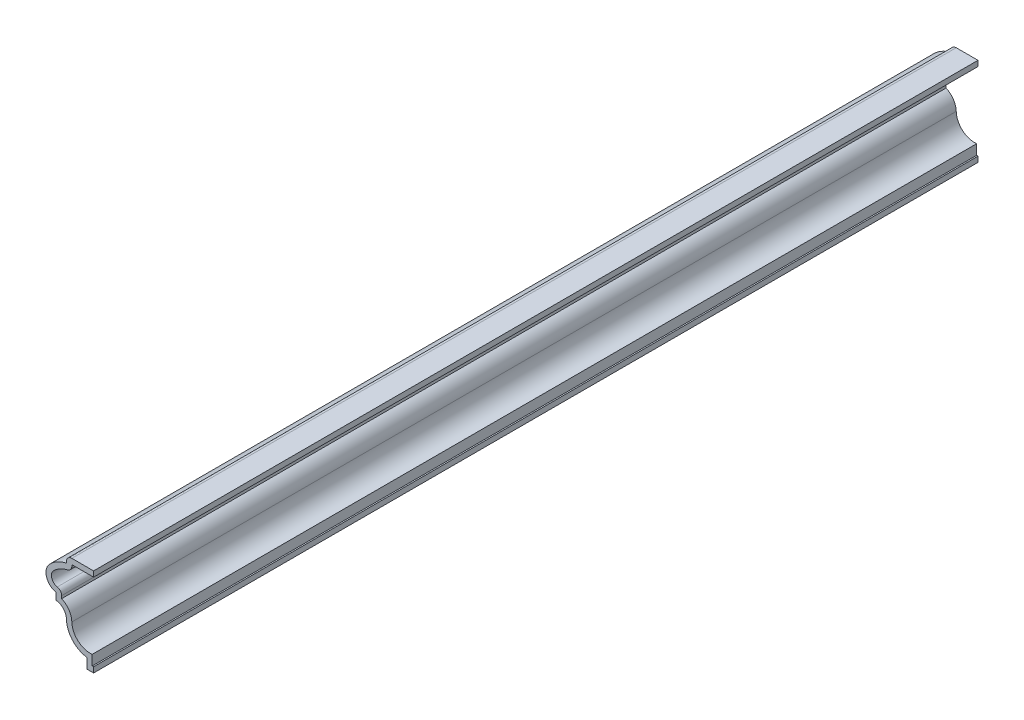
SolidWorks part; units mm, degrees
ref_plane "Front Plane" through (0, 0, 0) normal (0, 0, 1) x (1, 0, 0)
ref_plane "Top Plane" through (0, 0, 0) normal (0, 1, 0) x (1, 0, 0)
ref_plane "Right Plane" through (0, 0, 0) normal (1, 0, 0) x (0, 0, -1)
sketch "Sketch1" plane through (0, 0, 0) normal (0, 0, 1) x (1, 0, 0)
  line L0 (0, 0) -> (-1.5875, 0)
  line L1 (-1.5875, 0) -> (-1.5875, 2.3813)
  line L2 (-8.7312, 10.3187) -> (-8.7312, 11.9062)
  line L3 (-6.35, 19.05) -> (-6.35, 20.6375)
  line L4 (-6.35, 20.6375) -> (0, 20.6375)
  line L5 (-11.1125, 16.8312) -> (-11.1125, 12.2451) construction
  line L6 (31.4612, 165.4981) -> (216.1279, 165.4981) construction
  arc A0 (-1.5875, 2.3813) -> (-6.35, 7.7499) centre (-0.8035, 7.8734) cw
  arc A1 (-6.35, 7.7499) -> (-8.7312, 10.3187) centre (-8.9897, 7.6911) ccw
  arc A2 (-8.7312, 11.9062) -> (-10.2548, 16.8833) centre (-8.1603, 14.8027) cw
  arc A3 (-10.2548, 16.8833) -> (-6.35, 19.05) centre (-4.5651, 11.2315) cw
  point P13 (-0.7937, 0)
  point P16 (-11.1125, 14.8027)
  point P17 (-6.8154, 5.8928)
  point P18 (-6.0095, 5.8032)
  point P21 (0, 0)
  point P22 (-11.1125, 14.8027)
  point P25 (-6.35, 19.05)
  point P26 (-6.35, 7.6906)
  dimension "D12" = 5.5478
  dimension "D13" = 2.6403
  dimension "D14" = 2.9522
  dimension "D15" = 8.0197
  dimension "D1" = 6.35
  dimension "D2" = 1.5875
  dimension "D3" = 2.3813
  dimension "D4" = 1.5875
  dimension "D5" = 7.9375
  dimension "D6" = 7.1437
  dimension "D7" = 1.5875
  dimension "D8" = 20.6375
  dimension "D9" = 7.1437
  dimension "D10" = 11.1125
  dimension "D11" = 2.3813
extrude "Extrude-Thin1" add sketch "Sketch1" against normal blind 206.375 thin contours L0 L1 A0 A1 L2 A2 A3 L3 L4
fillet "Fillet1" radius 1.27 3 edges at (-7.4612, 13.2726, -103.1875) (-5.08, 17.9615, -103.1875) (-6.35, 20.6375, -103.1875)
